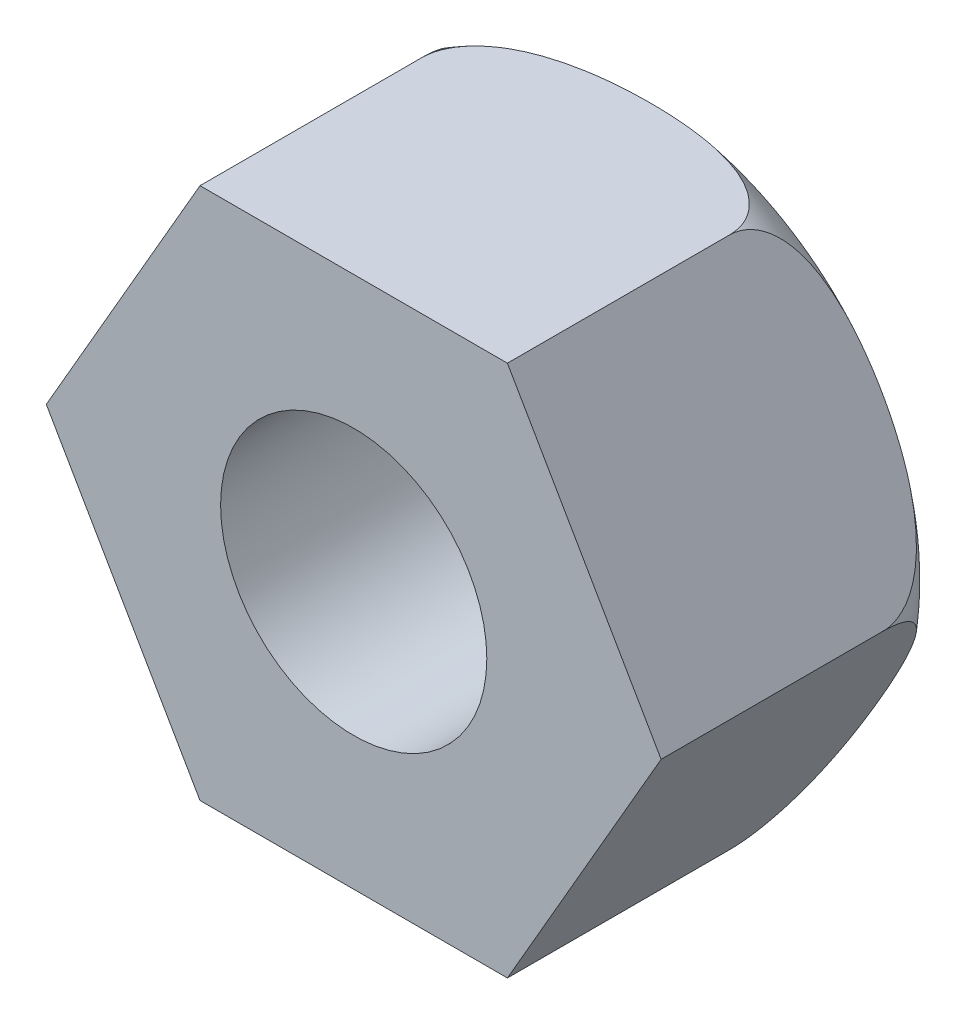
SolidWorks part; units mm, degrees
ref_plane "Front Plane" through (0, 0, 0) normal (0, 0, 1) x (1, 0, 0)
ref_plane "Top Plane" through (0, 0, 0) normal (0, 1, 0) x (1, 0, 0)
ref_plane "Right Plane" through (0, 0, 0) normal (1, 0, 0) x (0, 0, -1)
sketch "Sketch1" plane through (0, 0, 0) normal (0, 0, 1) x (1, 0, 0)
  line L1 (-34.641, 0) -> (-17.3205, -30)
  line L2 (-17.3205, -30) -> (17.3205, -30)
  line L3 (17.3205, -30) -> (34.641, 0)
  line L4 (34.641, 0) -> (17.3205, 30)
  line L5 (17.3205, 30) -> (-17.3205, 30)
  line L6 (-17.3205, 30) -> (-34.641, 0)
  circle A0 centre (0, 0) radius 30 construction
  dimension "D1" = 60
extrude "Boss-Extrude1" add sketch "Sketch1" along normal blind 35
sketch "Sketch2" plane through (0, 0, 35) normal (0, 0, 1) x (1, 0, 0)
  circle A0 centre (0, 0) radius 15
  dimension "D1" = 30
extrude "Cut-Extrude1" cut sketch "Sketch2" against normal blind 35
sketch "Sketch3" plane through (0, 0, 0) normal (0, 1, 0) x (1, 0, 0)
  line L0 (34.641, 0) -> (17.3205, 0) construction
  line L1 (34.641, -35) -> (34.641, 0) construction
  line L2 (24.641, 0) -> (34.641, 0)
  line L3 (34.641, 0) -> (34.641, -10)
  arc A0 (24.641, 0) -> (34.641, -10) centre (24.641, -10) cw
  dimension "D1" = 10
revolve "Cut-Revolve1" cut sketch "Sketch3" angle 360 about axis through (0, 0, 0) along (0, 0, 1)
